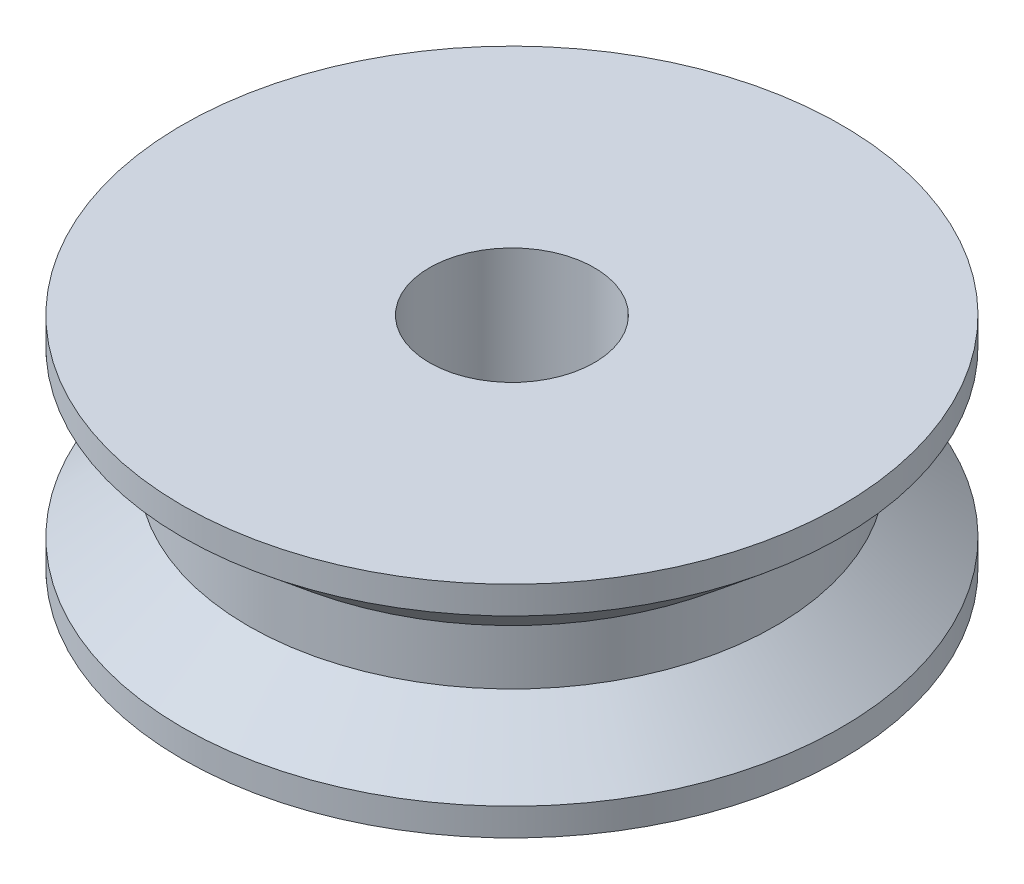
SolidWorks part; units mm, degrees
ref_plane "Front Plane" through (0, 0, 0) normal (0, 0, 1) x (1, 0, 0)
ref_plane "Top Plane" through (0, 0, 0) normal (0, 1, 0) x (1, 0, 0)
ref_plane "Right Plane" through (0, 0, 0) normal (1, 0, 0) x (0, 0, -1)
sketch "Sketch1" plane through (0, 0, 0) normal (0, 1, 0) x (1, 0, 0)
  circle A0 centre (0, 0) radius 6
  circle A1 centre (0, 0) radius 1.5
  dimension "D1" = 3
  dimension "D2" = 12
extrude "Main Body" add sketch "Sketch1" along normal blind 4
sketch "Sketch6" plane through (0, 0, 0) normal (0, 0, 1) x (1, 0, 0)
  line L4 (6, 0.5) -> (6, 3.5)
  line L6 (4.8, 2.5) -> (4.8, 1.5)
  line L7 (4.8, 2.5) -> (6, 3.5)
  line L8 (4.8, 1.5) -> (6, 0.5)
  dimension "D1" = 4.8
  dimension "D2" = 6
  dimension "D3" = 0.5
  dimension "D4" = 1.5
  dimension "D5" = 2.5
revolve "Tendon Guide" cut sketch "Sketch6" angle 360 about axis through (0, 4, 0) along (0, -1, 0)
